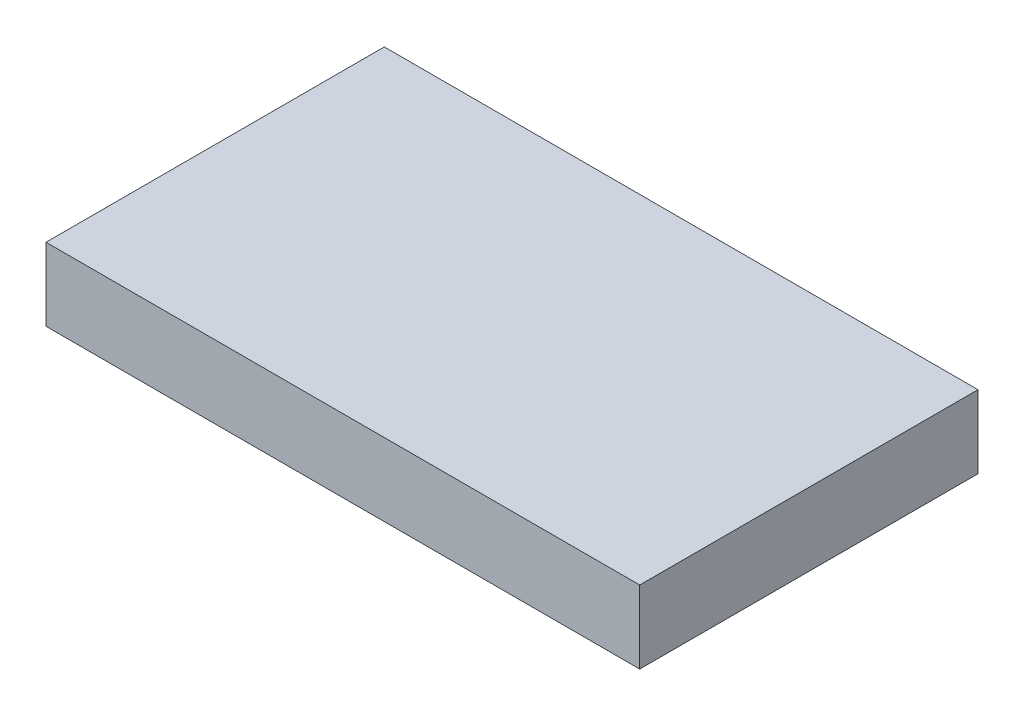
SolidWorks part; units mm, degrees
ref_plane "Front Plane" through (0, 0, 0) normal (0, 0, 1) x (1, 0, 0)
ref_plane "Top Plane" through (0, 0, 0) normal (0, 1, 0) x (1, 0, 0)
ref_plane "Right Plane" through (0, 0, 0) normal (1, 0, 0) x (0, 0, -1)
sketch "Sketch1" plane through (0, 0, 0) normal (0, 1, 0) x (1, 0, 0)
  line L1 (-26.5, -15.1) -> (26.5, -15.1)
  line L2 (-26.5, -15.1) -> (-26.5, 15.1)
  line L3 (-26.5, 15.1) -> (26.5, 15.1)
  line L4 (26.5, -15.1) -> (26.5, 15.1)
  line L5 (-26.5, -15.1) -> (26.5, 15.1) construction
  line L6 (-26.5, 15.1) -> (26.5, -15.1) construction
  point P0 (0, 0)
  dimension "D1" = 53
  dimension "D2" = 30.2
extrude "Boss-Extrude1" add sketch "Sketch1" along normal blind 6.5
